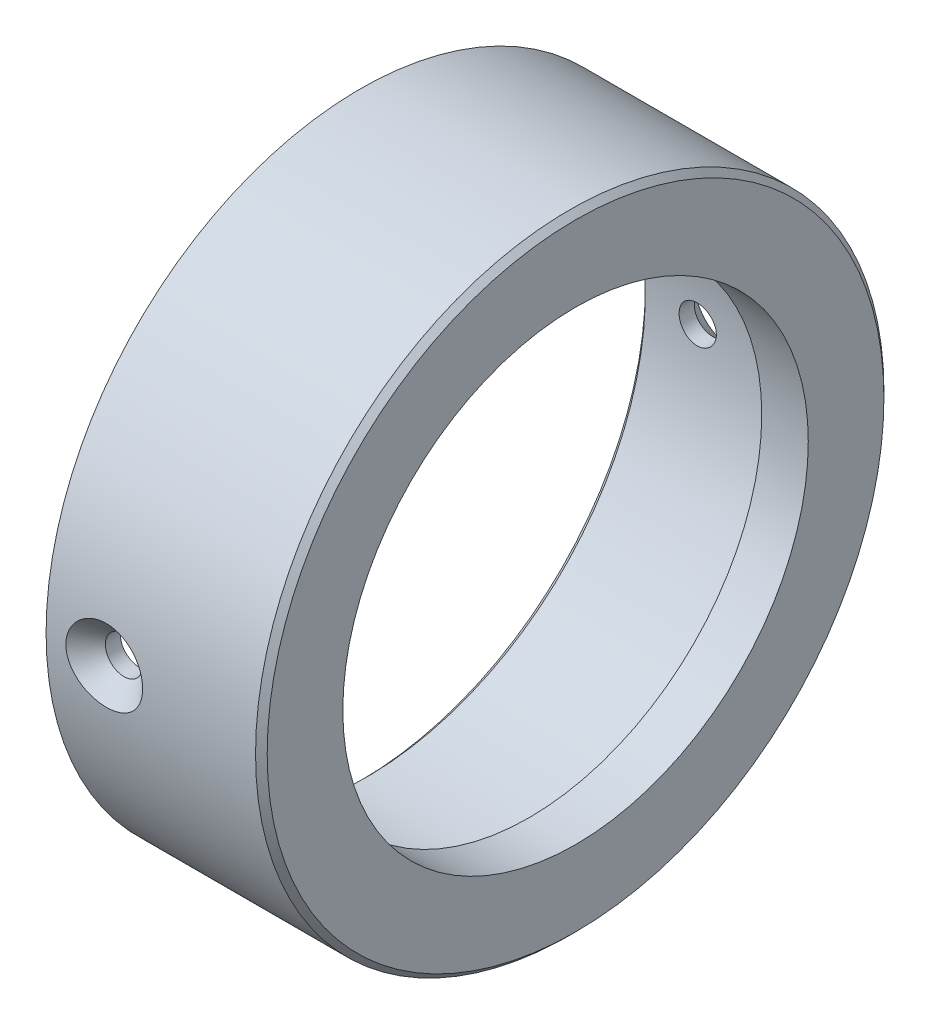
SolidWorks part; units mm, degrees
ref_plane "Přední rovina" through (0, 0, 0) normal (0, 0, 1) x (1, 0, 0)
ref_plane "Horní rovina" through (0, 0, 0) normal (0, 1, 0) x (1, 0, 0)
ref_plane "Pravá rovina" through (0, 0, 0) normal (1, 0, 0) x (0, 0, -1)
sketch "Skica1" plane through (0, 0, 0) normal (0, 0, 1) x (1, 0, 0)
  line L0 (-342.05, 21.5) -> (-342.05, -21.5) construction
  line L1 (-342.05, 21.5) -> (-342.05, -21.5) construction
  line L2 (-350.05, -20) -> (-344.05, -20) construction
  line L3 (-350.05, -20) -> (-344.05, -20) construction
  line L4 (-346.05, -20) -> (-342.05, -20)
  line L6 (-342.05, -20) -> (-342.05, -27)
  line L7 (-342.05, -27) -> (-360.55, -27)
  line L8 (-360.55, -27) -> (-360.55, -24)
  line L9 (-360.55, -24) -> (-346.05, -24)
  line L10 (-346.05, -24) -> (-346.05, -20)
  line L12 (-506.9511, 0) -> (94.0461, 0) construction
  line L13 (-365.55, -21) -> (-365.55, 21) construction
  line L14 (-390.1185, 0) -> (-358.6078, 0) construction
  dimension "D1" = 20
  dimension "D2" = 4
  dimension "D3" = 5
  dimension "D4" = 4
  dimension "D5" = 3
revolve "Rotovat1" add sketch "Skica1" angle 360 about L14
chamfer "Zkosení1" distance 0.5 angle 45 2 edges at (-342.05, 0, 27) (-360.55, 0, 24)
chamfer "Zkosení2" distance 0.5 angle 45 1 edges at (-346.05, 0, 24)
ref_plane "Rovina1" through (0, 0, -27) normal (0, 0, -1) x (-1, 0, 0)
sketch "Skica4" plane through (0, 0, -27) normal (0, 0, -1) x (-1, 0, 0)
  point P0 (355.55, 0)
hole_wizard "Kuželové zahloubení pro M3 šroubu se zápustnou hlavou plochou1" positions "3DSkica3" profile "Skica3" countersink size "M3" standard "ISO"
sketch3d "3DSkica3"
  point P0 (-355.55, 0, -27)
sketch "Skica3" plane through (-355.55, 0, -27) normal (1, 0, 0) x (0, 1, 0)
  line L0 (0, 0) -> (0, 54)
  line L1 (0, 54) -> (1.6, 54)
  line L2 (1.6, 54) -> (1.6, 1.7)
  line L3 (1.6, 1.7) -> (3.3, 0)
  line L5 (3.3, 0) -> (0, 0)
  line L6 (-1.6, 1.7) -> (-3.3, 0) construction
  line L11 (0, -6.35) -> (0, 107.95) construction
  dimension "Průměr díry skrz" = 3.2
  dimension "Hloubka díry skrz" = 54
  dimension "Průměr blíz. kuž. zahloubení" = 6.6
  dimension "Úhel blíz. kuž. zahloubení" = 90
pattern_circular "Kruhové pole1" count 2 every 180 of "Kuželové zahloubení pro M3 šroubu se zápustnou hlavou plochou1"
